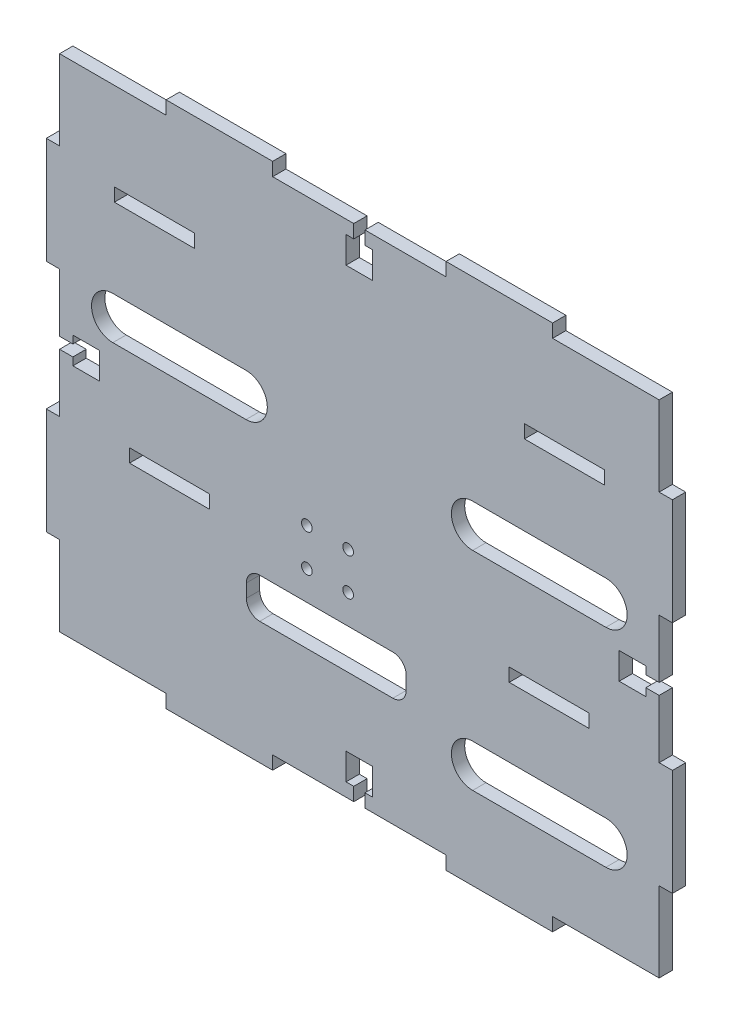
SolidWorks part; units mm, degrees
ref_plane "Front Plane" through (0, 0, 0) normal (0, 0, 1) x (1, 0, 0)
ref_plane "Top Plane" through (0, 0, 0) normal (0, 1, 0) x (1, 0, 0)
ref_plane "Right Plane" through (0, 0, 0) normal (1, 0, 0) x (0, 0, -1)
sketch "Sketch1" plane through (0, 0, 0) normal (0, 0, 1) x (1, 0, 0)
  line L1 (112.555, -94) -> (-112.555, -94)
  line L2 (112.555, -94) -> (112.555, 94)
  line L3 (112.555, 94) -> (-112.555, 94)
  line L4 (-112.555, -94) -> (-112.555, 94)
  line L5 (112.555, -94) -> (-112.555, 94) construction
  line L6 (112.555, 94) -> (-112.555, -94) construction
  point P0 (0, 0)
  dimension "D1" = 188
  dimension "D2" = 225.11
extrude "Boss-Extrude1" add sketch "Sketch1" along normal blind 5
sketch "Sketch2" plane through (0, 0, 5) normal (0, 0, 1) x (1, 0, 0)
  circle A0 centre (-19.7145, -13) radius 2
  circle A1 centre (-4.2145, -13) radius 2
  circle A2 centre (-4.2145, -27) radius 2
  circle A3 centre (-19.7145, -27) radius 2
extrude "Cut-Extrude1" cut sketch "Sketch2" against normal blind 10
sketch "Sketch3" plane through (0, -94, 0) normal (0, -1, 0) x (1, 0, 0)
  line L0 (-112.555, 5) -> (112.555, 5) construction
  line L1 (-72.555, 5) -> (-32.555, 5)
  line L2 (-72.555, 5) -> (-72.555, 0)
  line L3 (-72.555, 0) -> (-32.555, 0)
  line L4 (-32.555, 5) -> (-32.555, 0)
  line L5 (-112.555, 0) -> (112.555, 0) construction
  line L6 (-112.555, 5) -> (-112.555, 0) construction
  line L7 (32.555, 5) -> (72.555, 5)
  line L8 (32.555, 5) -> (32.555, 0)
  line L9 (32.555, 0) -> (72.555, 0)
  line L10 (72.555, 5) -> (72.555, 0)
  line L11 (112.555, 5) -> (112.555, 0) construction
  dimension "D1" = 40
  dimension "D2" = 40
  dimension "D3" = 40
  dimension "D4" = 40
extrude "Boss-Extrude2" add sketch "Sketch3" along normal blind 5
sketch "Sketch5" plane through (0, 0, 5) normal (0, 0, 1) x (1, 0, 0)
  line L0 (112.555, -94) -> (112.555, 94) construction
  line L1 (112.555, -64) -> (117.555, -64)
  line L2 (112.555, -64) -> (112.555, -24)
  line L3 (112.555, -24) -> (117.555, -24)
  line L4 (117.555, -64) -> (117.555, -24)
  line L5 (112.541, -94) -> (112.541, 91.198) construction
  line L6 (112.541, 24) -> (117.541, 24)
  line L7 (112.541, 24) -> (112.541, 64)
  line L8 (112.541, 64) -> (117.541, 64)
  line L9 (117.541, 24) -> (117.541, 64)
  line L10 (112.555, 94) -> (-112.555, 94) construction
  line L11 (72.555, 94) -> (32.555, 94)
  line L12 (72.555, 94) -> (72.555, 99)
  line L13 (72.555, 99) -> (32.555, 99)
  line L14 (32.555, 94) -> (32.555, 99)
  line L15 (72.555, -94) -> (112.555, -94) construction
  line L16 (-72.555, 94) -> (-32.555, 94)
  line L17 (-72.555, 94) -> (-72.555, 99)
  line L18 (-72.555, 99) -> (-32.555, 99)
  line L19 (-32.555, 94) -> (-32.555, 99)
  line L20 (0, -94) -> (0, -60.3386) construction
  line L21 (-32.555, -94) -> (32.555, -94) construction
  line L22 (-112.555, 94) -> (-112.555, -94) construction
  line L23 (-117.541, 24) -> (-117.541, 64)
  line L24 (-112.541, 64) -> (-117.541, 64)
  line L25 (-112.541, 24) -> (-112.541, 64)
  line L26 (-112.541, 24) -> (-117.541, 24)
  line L27 (-117.555, -64) -> (-117.555, -24)
  line L28 (-112.555, -24) -> (-117.555, -24)
  line L29 (-112.555, -64) -> (-112.555, -24)
  line L30 (-112.555, -64) -> (-117.555, -64)
  point P22 (112.555, -44)
  point P25 (112.541, 44)
  point P31 (-72.555, 96.5)
  dimension "D1" = 5
  dimension "D2" = 40
  dimension "D3" = 30
  dimension "D4" = 5
  dimension "D5" = 40
  dimension "D6" = 30
  dimension "D7" = 5
  dimension "D8" = 5
  dimension "D9" = 40
  dimension "D10" = 40
  dimension "D11" = 40
  dimension "D12" = 40
extrude "Boss-Extrude3" add sketch "Sketch5" against normal blind 5
sketch "Sketch6" plane through (0, 0, 5) normal (0, 0, 1) x (1, 0, 0)
  line L0 (0, -94) -> (0, -74.3797) construction
  line L1 (-32.555, -94) -> (32.555, -94) construction
  line L2 (112.555, 0) -> (93.327, 0) construction
  line L3 (112.555, -24) -> (112.555, 24) construction
  line L4 (112.555, -2.1) -> (107.555, -2.1)
  line L5 (107.555, -2.1) -> (107.555, -5)
  line L6 (107.555, -5) -> (97.555, -5)
  line L7 (97.555, -5) -> (97.555, 5)
  line L8 (112.555, -2.1) -> (112.555, 2.1)
  line L9 (107.555, 5) -> (97.555, 5)
  line L10 (107.555, 2.1) -> (107.555, 5)
  line L11 (112.555, 2.1) -> (107.555, 2.1)
  line L12 (2.1, -94) -> (2.1, -89)
  line L13 (2.1, -89) -> (5, -89)
  line L14 (5, -89) -> (5, -79)
  line L15 (5, -79) -> (-5, -79)
  line L16 (2.1, -94) -> (-2.1, -94)
  line L17 (-5, -89) -> (-5, -79)
  line L18 (-2.1, -89) -> (-5, -89)
  line L19 (-2.1, -94) -> (-2.1, -89)
  line L20 (0, 94) -> (0, 74.3797) construction
  line L21 (-2.1, 94) -> (-2.1, 89)
  line L22 (-2.1, 89) -> (-5, 89)
  line L23 (-5, 89) -> (-5, 79)
  line L24 (2.1, 94) -> (-2.1, 94)
  line L25 (5, 79) -> (-5, 79)
  line L26 (5, 89) -> (5, 79)
  line L27 (2.1, 89) -> (5, 89)
  line L28 (2.1, 94) -> (2.1, 89)
  line L29 (-112.555, 0) -> (-93.327, 0) construction
  line L30 (-112.555, 2.1) -> (-107.555, 2.1)
  line L31 (-107.555, 2.1) -> (-107.555, 5)
  line L32 (-107.555, 5) -> (-97.555, 5)
  line L33 (-112.555, -2.1) -> (-112.555, 2.1)
  line L34 (-97.555, -5) -> (-97.555, 5)
  line L35 (-107.555, -5) -> (-97.555, -5)
  line L36 (-107.555, -2.1) -> (-107.555, -5)
  line L37 (-112.555, -2.1) -> (-107.555, -2.1)
  point P15 (97.555, 0)
  point P25 (0, -79)
  point P37 (0, 79)
  point P48 (-97.555, 0)
  dimension "D1" = 2.1
  dimension "D2" = 5
  dimension "D3" = 10
  dimension "D4" = 5
  dimension "D5" = 2.1
  dimension "D6" = 5
  dimension "D7" = 5
  dimension "D8" = 10
extrude "Cut-Extrude2" cut sketch "Sketch6" against normal blind 5
sketch "Sketch7" plane through (0, 0, 5) normal (0, 0, 1) x (1, 0, 0)
  line L0 (0.7855, -38) -> (-25.6145, -38)
  line L1 (-12.4145, -38) -> (-12.4145, -59.2753) construction
  line L2 (12.5855, -53) -> (-37.4145, -53)
  line L3 (17.5855, -48) -> (17.5855, -43)
  line L4 (12.5855, -38) -> (-37.4145, -38)
  line L5 (-42.4145, -48) -> (-42.4145, -43)
  arc A0 (-37.4145, -38) -> (-42.4145, -43) centre (-37.4145, -43) ccw
  arc A1 (-37.4145, -53) -> (-42.4145, -48) centre (-37.4145, -48) cw
  arc A2 (17.5855, -43) -> (12.5855, -38) centre (12.5855, -43) ccw
  arc A3 (12.5855, -53) -> (17.5855, -48) centre (12.5855, -48) ccw
  point P10 (-12.4145, -53)
  point P15 (-42.4145, -53)
  point P18 (17.5855, -38)
  point P21 (17.5855, -53)
  dimension "D3" = 5
  dimension "D1" = 60
  dimension "D2" = 15
extrude "Cut-Extrude3" cut sketch "Sketch7" against normal blind 5 contours L0 L1 L2 A3 L3 A2 L4 | L1 L4 A0 L5 A1 L2
sketch "Sketch8" plane through (0, 0, 5) normal (0, 0, 1) x (1, 0, 0)
  line L1 (86.2702, -26) -> (56.2702, -26)
  line L2 (86.2702, -26) -> (86.2702, -21)
  line L3 (86.2702, -21) -> (56.2702, -21)
  line L4 (56.2702, -26) -> (56.2702, -21)
  line L5 (-56.2992, -26) -> (-86.2992, -26)
  line L6 (-56.2992, -26) -> (-56.2992, -21)
  line L7 (-56.2992, -21) -> (-86.2992, -21)
  line L8 (-86.2992, -26) -> (-86.2992, -21)
extrude "Cut-Extrude4" cut sketch "Sketch8" against normal blind 5
sketch "Sketch9" plane through (0, 0, 0) normal (0, 0, -1) x (-1, 0, 0)
  line L0 (0, 79) -> (0, 49.3621) construction
  line L1 (91.9848, 56) -> (61.9848, 56)
  line L2 (91.9848, 56) -> (91.9848, 61)
  line L3 (91.9848, 61) -> (61.9848, 61)
  line L4 (61.9848, 56) -> (61.9848, 61)
  line L5 (5, 79) -> (-5, 79) construction
  line L6 (-61.9848, 56) -> (-61.9848, 61)
  line L7 (-91.9848, 61) -> (-61.9848, 61)
  line L8 (-91.9848, 56) -> (-91.9848, 61)
  line L9 (-91.9848, 56) -> (-61.9848, 56)
extrude "Cut-Extrude5" cut sketch "Sketch9" against normal blind 5
sketch "Sketch10" plane through (0, 0, 5) normal (0, 0, 1) x (1, 0, 0)
  line L0 (112.555, -94) -> (112.555, -26) construction
  line L1 (86.2702, -26) -> (112.555, -26) construction
  line L2 (112.555, -60) -> (33.8613, -60) construction
  line L3 (92.555, -60) -> (42.555, -60) construction
  line L4 (92.555, -68) -> (42.555, -68)
  line L5 (92.555, -52) -> (42.555, -52)
  line L6 (0, 79) -> (0, -79) construction
  line L7 (-5, 79) -> (5, 79) construction
  line L8 (5, -79) -> (-5, -79) construction
  line L9 (91.9848, 56) -> (91.9848, -19.9132) construction
  line L10 (91.9848, 18.0434) -> (21.2965, 18.0434) construction
  line L11 (92.555, 18.0434) -> (42.555, 18.0434) construction
  line L12 (92.555, 10.0434) -> (42.555, 10.0434)
  line L13 (92.555, 26.0434) -> (42.555, 26.0434)
  line L14 (112.555, 2.1) -> (112.555, 24) construction
  line L15 (-91.9848, 18.0434) -> (-21.2965, 18.0434) construction
  line L16 (-112.555, -60) -> (-33.8613, -60) construction
  line L17 (-112.555, -94) -> (-112.555, -26) construction
  line L18 (-92.555, 18.0434) -> (-42.555, 18.0434) construction
  line L19 (-92.555, 10.0434) -> (-42.555, 10.0434)
  line L20 (-92.555, 26.0434) -> (-42.555, 26.0434)
  line L21 (-92.555, -60) -> (-42.555, -60) construction
  line L22 (-92.555, -68) -> (-42.555, -68)
  line L23 (-92.555, -52) -> (-42.555, -52)
  arc A0 (92.555, -68) -> (92.555, -52) centre (92.555, -60) ccw
  arc A1 (42.555, -52) -> (42.555, -68) centre (42.555, -60) ccw
  arc A2 (92.555, 10.0434) -> (92.555, 26.0434) centre (92.555, 18.0434) ccw
  arc A3 (42.555, 26.0434) -> (42.555, 10.0434) centre (42.555, 18.0434) ccw
  arc A4 (-92.555, 10.0434) -> (-92.555, 26.0434) centre (-92.555, 18.0434) cw
  arc A5 (-42.555, 26.0434) -> (-42.555, 10.0434) centre (-42.555, 18.0434) cw
  arc A6 (-92.555, -68) -> (-92.555, -52) centre (-92.555, -60) cw
  arc A7 (-42.555, -52) -> (-42.555, -68) centre (-42.555, -60) cw
  point P9 (67.555, -60)
  point P28 (67.555, 18.0434)
  point P43 (-67.555, 18.0434)
  point P50 (-67.555, -60)
  dimension "D1" = 8
  dimension "D4" = 8
  dimension "D2" = 50
  dimension "D3" = 20
  dimension "D5" = 50
  dimension "D6" = 20
extrude "Cut-Extrude6" cut sketch "Sketch10" against normal blind 15
sketch "Sketch11" plane through (0, 0, 5) normal (0, 0, 1) x (1, 0, 0)
  line L0 (-92.555, -68) -> (-42.555, -68) construction
  line L1 (-42.555, -52) -> (-92.555, -52) construction
  line L2 (-92.555, -68) -> (-42.555, -68)
  line L3 (-42.555, -52) -> (-92.555, -52)
  arc A0 (-92.555, -52) -> (-92.555, -68) centre (-92.555, -60) ccw construction
  arc A1 (-42.555, -68) -> (-42.555, -52) centre (-42.555, -60) ccw construction
  arc A2 (-92.555, -52) -> (-92.555, -68) centre (-92.555, -60) ccw
  arc A3 (-42.555, -68) -> (-42.555, -52) centre (-42.555, -60) ccw
extrude "Boss-Extrude4" add sketch "Sketch11" against normal blind 5
